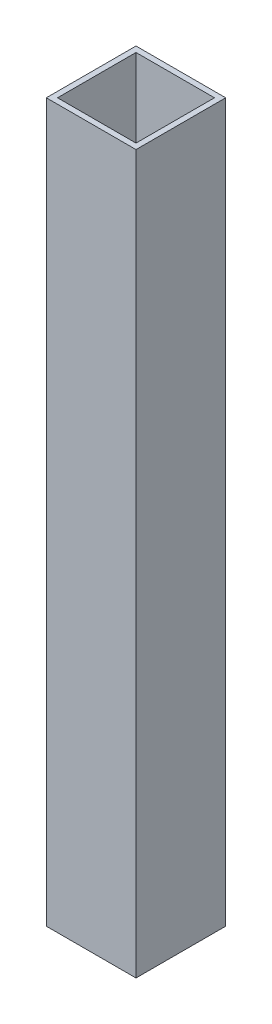
SolidWorks part; units mm, degrees
material "6061 Alloy"
ref_plane "Front Plane" through (0, 0, 0) normal (0, 0, 1) x (1, 0, 0)
ref_plane "Top Plane" through (0, 0, 0) normal (0, 1, 0) x (1, 0, 0)
ref_plane "Right Plane" through (0, 0, 0) normal (1, 0, 0) x (0, 0, -1)
sketch "Sketch1" plane through (0, 0, 0) normal (0, 1, 0) x (1, 0, 0)
  line L0 (-11.1125, 11.1125) -> (-11.1125, -11.1125)
  line L1 (12.7, 12.7) -> (-12.7, 12.7)
  line L2 (12.7, 12.7) -> (12.7, -12.7)
  line L3 (12.7, -12.7) -> (-12.7, -12.7)
  line L4 (-12.7, 12.7) -> (-12.7, -12.7)
  line L5 (12.7, 12.7) -> (-12.7, -12.7) construction
  line L6 (12.7, -12.7) -> (-12.7, 12.7) construction
  line L7 (11.1125, -11.1125) -> (-11.1125, -11.1125)
  line L8 (11.1125, 11.1125) -> (11.1125, -11.1125)
  line L9 (11.1125, 11.1125) -> (-11.1125, 11.1125)
  point P0 (0, 0)
  dimension "D1" = 25.4
  dimension "D2" = 1.5875
extrude "Boss-Extrude1" add sketch "Sketch1" along normal blind 203.2
